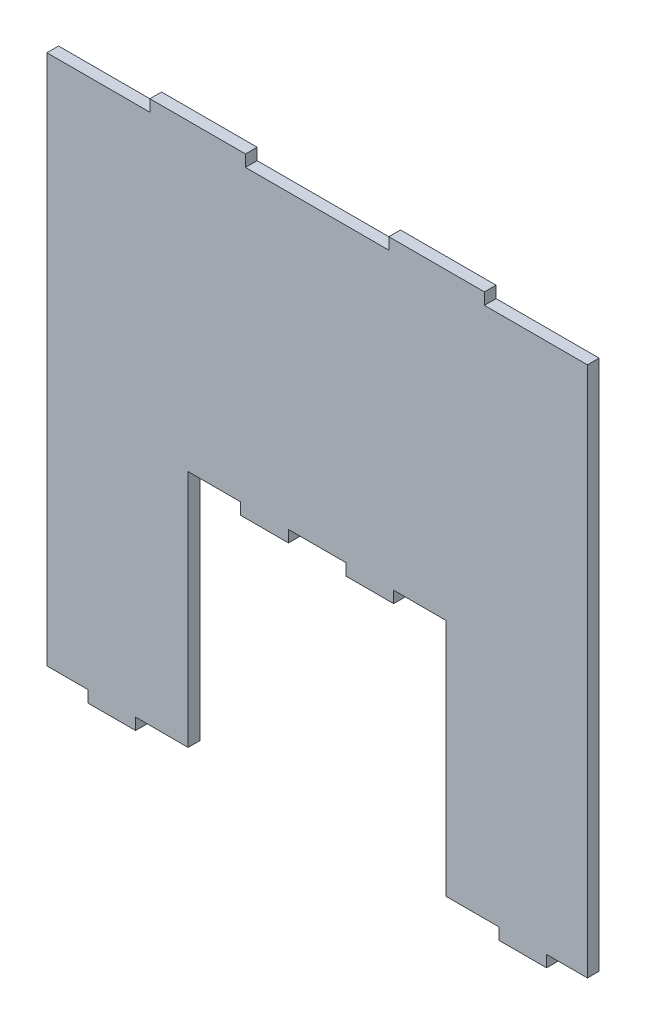
SolidWorks part; units mm, degrees
ref_plane "Alzado" through (0, 0, 0) normal (0, 0, 1) x (1, 0, 0)
ref_plane "Planta" through (0, 0, 0) normal (0, 1, 0) x (1, 0, 0)
ref_plane "Vista lateral" through (0, 0, 0) normal (1, 0, 0) x (0, 0, -1)
sketch "Croquis1" plane through (0, 0, 0) normal (0, 0, 1) x (1, 0, 0)
  line L0 (-27, -55.56) -> (27, -55.56) construction
  line L1 (-56.56, -55.56) -> (-48, -55.56)
  line L2 (-56.56, -55.56) -> (-56.56, 55.56)
  line L3 (-56.56, 55.56) -> (-35, 55.56)
  line L4 (56.56, -55.56) -> (56.56, 55.56)
  line L5 (-56.56, -55.56) -> (56.56, 55.56) construction
  line L6 (-56.56, 55.56) -> (56.56, -55.56) construction
  line L7 (27, -55.56) -> (27, -5.56)
  line L8 (27, -5.56) -> (16, -5.56)
  line L9 (-27, -5.56) -> (-27, -55.56)
  line L10 (27, -55.56) -> (38, -55.56)
  line L11 (0, 0) -> (0, -55.56) construction
  line L12 (48, -55.56) -> (56.56, -55.56)
  line L13 (48, -58) -> (38, -58)
  line L14 (48, -58) -> (48, -55.56)
  line L15 (-38, -58) -> (-38, -55.56)
  line L16 (38, -58) -> (38, -55.56)
  line L17 (48, -58) -> (38, -55.56) construction
  line L18 (48, -55.56) -> (38, -58) construction
  line L19 (-48, -58) -> (-38, -58)
  line L20 (-48, -58) -> (-48, -55.56)
  line L21 (-38, -55.56) -> (-27, -55.56)
  line L22 (35, 55.56) -> (56.56, 55.56)
  line L23 (35, 58) -> (15, 58)
  line L24 (35, 58) -> (35, 55.56)
  line L25 (-35, 58) -> (-35, 55.56)
  line L26 (15, 58) -> (15, 55.56)
  line L27 (35, 58) -> (15, 55.56) construction
  line L28 (35, 55.56) -> (15, 58) construction
  line L29 (-35, 58) -> (-15, 58)
  line L30 (-15, 58) -> (-15, 55.56)
  line L31 (-15, 55.56) -> (15, 55.56)
  line L32 (-16, -5.56) -> (-27, -5.56)
  line L33 (6, -5.56) -> (-6, -5.56)
  line L34 (-16, -5.56) -> (-16, -8)
  line L35 (-16, -8) -> (-6, -8)
  line L36 (-6, -5.56) -> (-6, -8)
  line L38 (6, -5.56) -> (6, -8)
  line L39 (6, -8) -> (16, -8)
  line L40 (16, -5.56) -> (16, -8)
  point P0 (0, 0)
  point P8 (0, -55.56)
  point P11 (43, -56.78)
  point P22 (25, 56.78)
  dimension "D1" = 111.12
  dimension "D2" = 113.12
  dimension "D3" = 54
  dimension "D4" = 50
  dimension "D5" = 38
  dimension "D6" = 10
  dimension "D7" = 2.44
  dimension "D8" = 15
  dimension "D9" = 20
  dimension "D10" = 2.44
  dimension "D11" = 6
  dimension "D12" = 10
  dimension "D13" = 6
  dimension "D14" = 10
  dimension "D15" = 2.44
  dimension "D16" = 2.44
extrude "Saliente-Extruir1" add sketch "Croquis1" along normal blind 2.44
